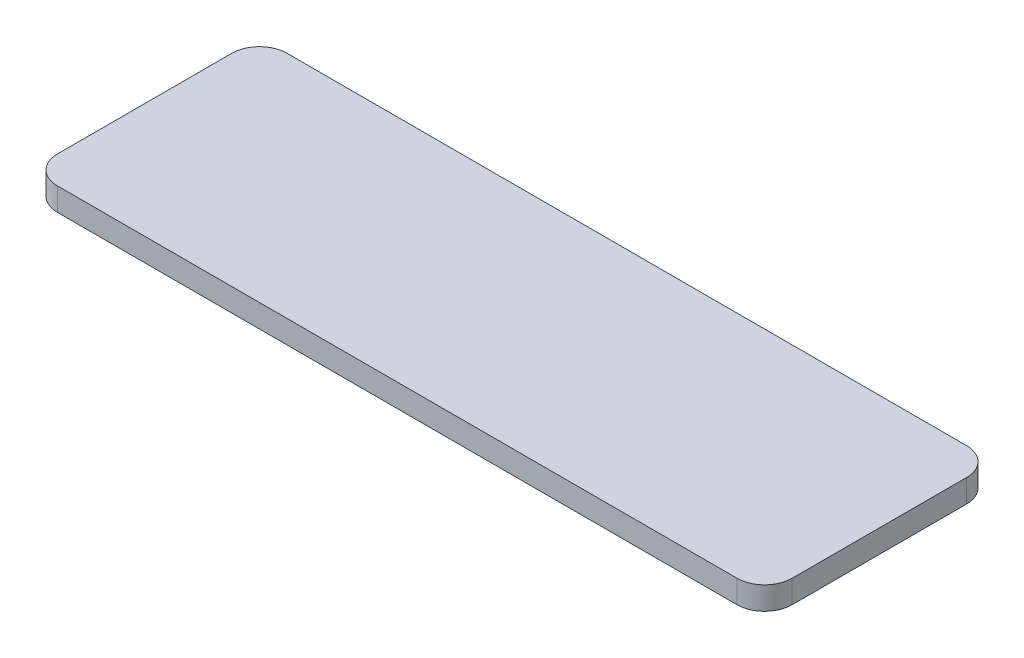
SolidWorks part; units mm, degrees
ref_plane "Front Plane" through (0, 0, 0) normal (0, 0, 1) x (1, 0, 0)
ref_plane "Top Plane" through (0, 0, 0) normal (0, 1, 0) x (1, 0, 0)
ref_plane "Right Plane" through (0, 0, 0) normal (1, 0, 0) x (0, 0, -1)
sketch "Sketch1" plane through (0, 0, 0) normal (0, 1, 0) x (1, 0, 0)
  line L0 (0, 0) -> (148, 0)
  line L1 (-6, -6) -> (-6, -44)
  line L2 (0, -50) -> (148, -50)
  line L3 (154, -6) -> (154, -44)
  arc A0 (154, -44) -> (148, -50) centre (148, -44) cw
  arc A1 (154, -6) -> (148, 0) centre (148, -6) ccw
  arc A2 (0, 0) -> (-6, -6) centre (0, -6) ccw
  arc A3 (0, -50) -> (-6, -44) centre (0, -44) cw
  dimension "D2" = 6
  dimension "D1" = 50
  dimension "D3" = 0
  dimension "D4" = 0
extrude "Boss-Extrude1" add sketch "Sketch1" along normal blind 5
